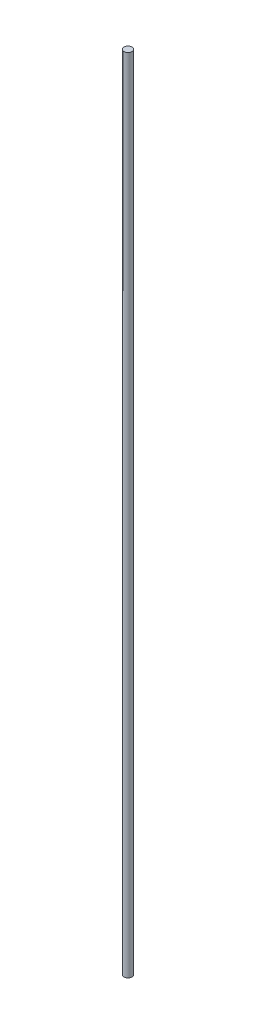
SolidWorks part; units mm, degrees
ref_plane "Front Plane" through (0, 0, 0) normal (0, 0, 1) x (1, 0, 0)
ref_plane "Top Plane" through (0, 0, 0) normal (0, 1, 0) x (1, 0, 0)
ref_plane "Right Plane" through (0, 0, 0) normal (1, 0, 0) x (0, 0, -1)
sketch "Sketch1" plane through (0, 0, 0) normal (0, 1, 0) x (1, 0, 0)
  circle A0 centre (0, 0) radius 20
  dimension "D1" = 40
extrude "Boss-Extrude1" add sketch "Sketch1" along normal blind 4000
